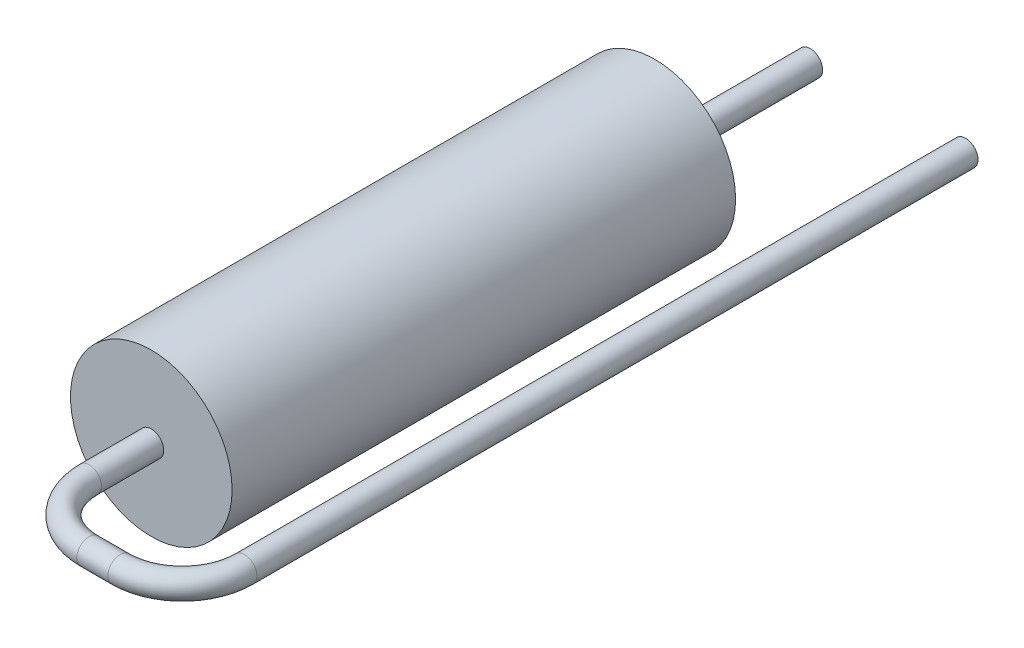
SolidWorks part; units mm, degrees
ref_plane "Front Plane" through (0, 0, 0) normal (0, 0, 1) x (1, 0, 0)
ref_plane "Top Plane" through (0, 0, 0) normal (0, 1, 0) x (1, 0, 0)
ref_plane "Right Plane" through (0, 0, 0) normal (1, 0, 0) x (0, 0, -1)
sketch "Sketch2" plane through (0, 0, 0) normal (0, 0, 1) x (1, 0, 0)
  circle A0 centre (0, 0) radius 2.6
  dimension "D1" = 5.2
extrude "Resistor Body" add sketch "Sketch2" along normal blind 16.2
sketch "Lead1 Path" plane through (0, 0, 0) normal (0, 1, 0) x (1, 0, 0)
  line L1 (-2.6, -16.2) -> (2.6, -16.2) construction
  line L2 (0, -16.2) -> (0, 0) construction
  line L3 (0, -16.2) -> (0, -18.2)
  line L4 (5, -18.2) -> (5, 5)
  line L5 (2, -20.2) -> (3, -20.2)
  arc A0 (0, -18.2) -> (2, -20.2) centre (2, -18.2) ccw
  arc A1 (5, -18.2) -> (3, -20.2) centre (3, -18.2) cw
  point P11 (0, -20.2)
  point P14 (5, -20.2)
  dimension "D4" = 2
  dimension "D1" = 25.2
  dimension "D2" = 4
  dimension "D3" = 5
sketch "Lead1 Profile" plane through (0, 0, 16.2) normal (0, 0, 1) x (-1, 0, 0)
  circle A0 centre (0, 0) radius 0.4
  dimension "D1" = 0.8
sweep "Lead1" add profiles "Lead1 Profile" path "Lead1 Path"
sketch "Sketch6" plane through (0, 0, 0) normal (0, 0, -1) x (1, 0, 0)
  circle A0 centre (0, 0) radius 0.4 construction
  circle A1 centre (0, 0) radius 0.4
extrude "Lead2" add sketch "Sketch6" along normal up to surface (5 mm away) up to face at (4.6, 0, -5)
ref_plane "Mounting Plane" through (0, 0, -1) normal (0, 0, 1) x (1, 0, 0)
sketch "Component_Outline" plane through (0, 0, -1) normal (0, 0, 1) x (1, 0, 0)
  line L0 (2.569, 0.4) -> (5, 0.4)
  line L1 (3, 0.4) -> (2, 0.4) construction
  line L2 (5, -0.4) -> (2.569, -0.4)
  arc A0 (2.569, 0.4) -> (2.569, -0.4) centre (0, 0) ccw
  arc A1 (5, 0.4) -> (5, -0.4) centre (5, 0) cw
  circle A2 centre (5, 0) radius 0.4 construction
  dimension "D1" = 2.6
